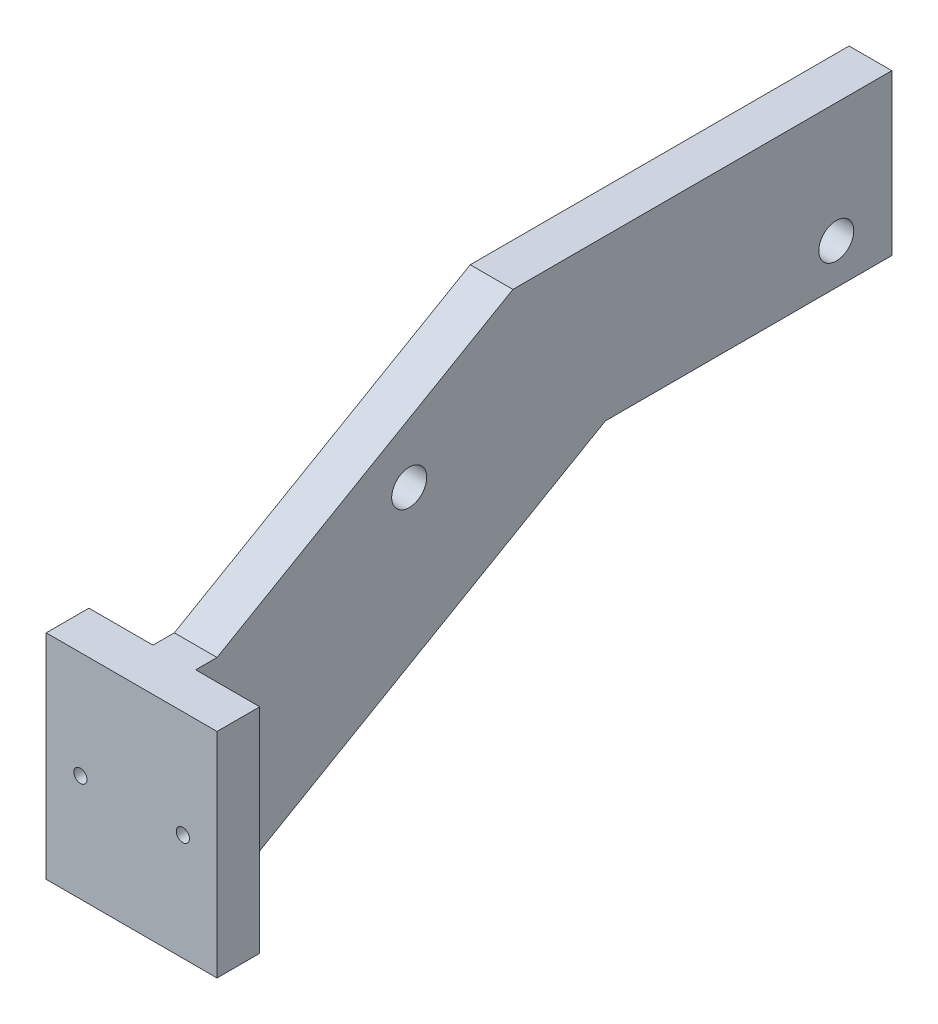
SolidWorks part; units mm, degrees
ref_plane "Alzado" through (0, 0, 0) normal (0, 0, 1) x (1, 0, 0)
ref_plane "Planta" through (0, 0, 0) normal (0, 1, 0) x (1, 0, 0)
ref_plane "Vista lateral" through (0, 0, 0) normal (1, 0, 0) x (0, 0, -1)
sketch "Croquis1" plane through (0, 0, 0) normal (1, 0, 0) x (0, 0, -1)
  line L0 (0, 0) -> (0, 50)
  line L1 (0, 50) -> (15, 50)
  line L2 (0, 0) -> (15, 0)
  line L3 (15, 0) -> (105.9327, 52.5)
  line L4 (15, 0) -> (40.1168, 0) construction
  line L5 (15, 50) -> (84.282, 90)
  line L7 (84.282, 90) -> (173.0021, 90)
  line L8 (173.0021, 90) -> (173.0021, 52.5)
  line L9 (173.0021, 52.5) -> (105.9327, 52.5)
  dimension "D1" = 50
  dimension "D2" = 15
  dimension "D3" = 30
  dimension "D4" = 15
  dimension "D5" = 80
  dimension "D6" = 67.0694
  dimension "D7" = 37.5
extrude "Saliente-Extruir1" add sketch "Croquis1" along normal blind 10
sketch "Croquis2" plane through (0, 0, 0) normal (0, 0, 1) x (1, 0, 0)
  line L0 (0, 50) -> (-15, 50)
  line L1 (-15, 50) -> (-15, 0)
  line L2 (-15, 0) -> (25, 0)
  line L3 (25, 0) -> (25, 50)
  line L4 (25, 50) -> (0, 50)
  dimension "D1" = 15
  dimension "D2" = 25
extrude "Saliente-Extruir2" add sketch "Croquis2" against normal blind 10
sketch "Croquis3" plane through (0, 0, 0) normal (0, 0, 1) x (1, 0, 0)
  circle A0 centre (-7, 25) radius 1.55
  circle A1 centre (17, 25) radius 1.55
  dimension "D2" = 3.1
  dimension "D3" = 3.1
  dimension "D1" = 24
  dimension "D4" = 8
  dimension "D5" = 25
extrude "Cortar-Extruir1" cut sketch "Croquis3" against normal blind 10
sketch "Croquis4" plane through (10, 0, 0) normal (1, 0, 0) x (0, 0, -1)
  circle A0 centre (60, 62) radius 4.1
  circle A1 centre (160, 62) radius 4.1
  dimension "D1" = 8.2
  dimension "D2" = 8.2
  dimension "D3" = 60
  dimension "D4" = 62
  dimension "D5" = 62
  dimension "D6" = 100
extrude "Cortar-Extruir2" cut sketch "Croquis4" against normal blind 10
